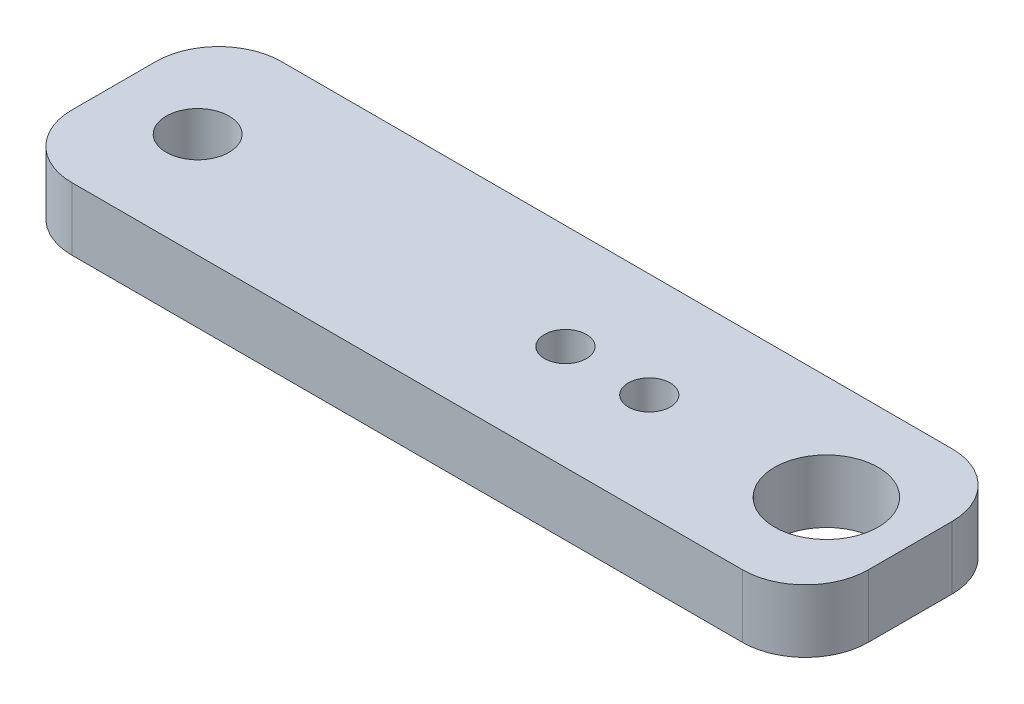
SolidWorks part; units mm, degrees
ref_plane "Front Plane" through (0, 0, 0) normal (0, 0, 1) x (1, 0, 0)
ref_plane "Top Plane" through (0, 0, 0) normal (0, 1, 0) x (1, 0, 0)
ref_plane "Right Plane" through (0, 0, 0) normal (1, 0, 0) x (0, 0, -1)
sketch "Sketch1" plane through (0, 0, 0) normal (0, 1, 0) x (1, 0, 0)
  line L1 (-19, 5) -> (19, 5)
  line L2 (-19, 5) -> (-19, -5)
  line L3 (-19, -5) -> (19, -5)
  line L4 (19, 5) -> (19, -5)
  line L5 (-19, 5) -> (19, -5) construction
  line L6 (-19, -5) -> (19, 5) construction
  point P0 (0, 0)
  dimension "D1" = 10
  dimension "D2" = 38
extrude "Boss-Extrude1" add sketch "Sketch1" along normal blind 3
sketch "Sketch2" plane through (0, 3, 0) normal (0, 1, 0) x (1, 0, 0)
  line L0 (15, 5) -> (15, -5) construction
  line L1 (-19, -5) -> (19, -5) construction
  line L2 (19, -5) -> (19, 5) construction
  circle A0 centre (15, 0) radius 2.4729
  circle A3 centre (6.55, 0) radius 1
  circle A4 centre (2.55, 0) radius 1
  point P10 (15, 0)
  dimension "D1" = 8.45
  dimension "D4" = 2
  dimension "D2" = 4
  dimension "D3" = 4
extrude "Cut-Extrude1" cut sketch "Sketch2" against normal blind 3
fillet "Fillet1" radius 3 4 edges at (19, 1.5, 5) (19, 1.5, -5) (-19, 1.5, -5) (-19, 1.5, 5)
hole_wizard "Ø3.0 (3) Diameter Hole1" positions "Sketch3" profile "Sketch4" hole size "Ø3.0" standard "BSI" end condition through all
sketch "Sketch3" plane through (0, 3, 0) normal (0, 1, 0) x (1, 0, 0)
  circle A1 centre (15, 0) radius 2.4729 construction
  point P0 (-15, 0)
  dimension "D1" = 30
sketch "Sketch4" plane through (-15, 3, 0) normal (1, 0, 0) x (0, 0, 1)
  line L0 (0, 0) -> (0, 3)
  line L1 (0, 3) -> (1.5, 3)
  line L2 (1.5, 3) -> (1.5, 0)
  line L5 (1.5, 0) -> (0, 0)
  line L11 (0, -6.35) -> (0, 107.95) construction
  dimension "Thru Hole Dia." = 3
  dimension "Thru Hole Depth" = 3
